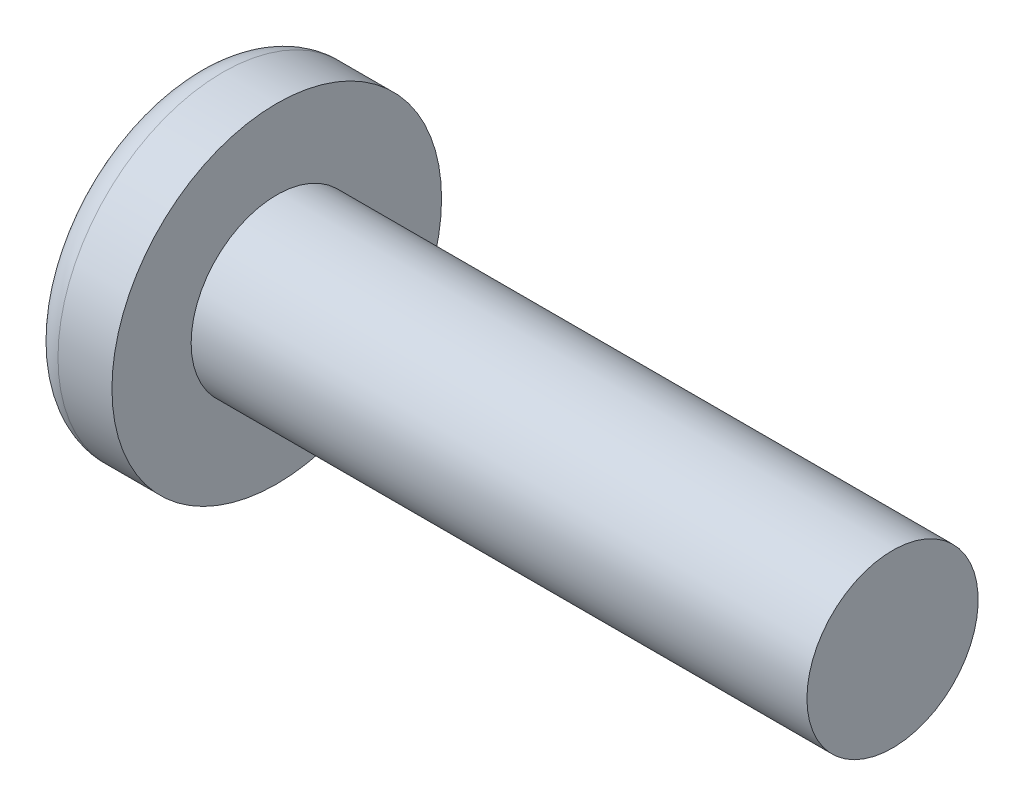
SolidWorks part; units mm, degrees
ref_plane "Plane1" through (0, 0, 0) normal (0, 0, 1) x (1, 0, 0)
ref_plane "Plane2" through (0, 0, 0) normal (0, 1, 0) x (1, 0, 0)
ref_plane "Plane3" through (0, 0, 0) normal (1, 0, 0) x (0, 0, -1)
sketch "BodySke" plane through (0, 0, 0) normal (0, 0, 1) x (1, 0, 0)
  line L0 (1.35, 1.065) -> (1.35, 2.05)
  line L1 (1.85, 6.35) -> (1.85, -3.175) construction
  line L2 (-25.4, 0) -> (127, 0) construction
  line L3 (9.01, 0) -> (0, 0)
  line L4 (1.35, 1.065) -> (9.01, 1.065)
  line L5 (9.01, 1.065) -> (9.01, 0)
  line L6 (0.6787, 2.05) -> (1.35, 2.05)
  line L7 (1.35, -1.065) -> (9.01, -1.065) construction
  line L8 (1.35, 6.35) -> (1.35, -3.175) construction
  arc A0 (0.3434, 1.8211) -> (0, 0) centre (5, 0) ccw
  arc A2 (0.3434, 1.8211) -> (0.6787, 2.05) centre (0.6787, 1.69) cw
  dimension "Head_crown_rad" = 5
  dimension "Head_fillet_rad" = 0.36
  dimension "Diameter" = 2.13
  dimension "Length" = 7.66
  dimension "Head_ht" = 1.35
  dimension "Head_dia" = 4.1
  dimension "Advance" = 0.5
  dimension "Thread_nom" = 7.66
revolve "Base-Revolve" add sketch "BodySke" angle 360 about L2
cosmetic thread "ThreadCosmetic" [suppressed] parameters "Thread_length"=7.16, "Thread_minor"=2.439
sketch "Sketch3" plane through (0, 0, 0) normal (1, 0, 0) x (0, 0, -1)
  line L0 (0.37, -1.45) -> (-0.37, -1.45)
  line L1 (0.37, -1.45) -> (0.37, 1.45)
  line L2 (-0.37, 1.45) -> (0.37, 1.45)
  line L3 (-0.37, 1.45) -> (-0.37, -1.45)
  dimension "Cross_dia" = 2.9
  dimension "D1" = 1.45
  dimension "Cross_width" = 0.74
  dimension "D2" = 0.37
ref_plane "Plane4" through (1.76, 0, 0) normal (1, 0, 0) x (0, 0, -1)
sketch "Sketch4" plane through (1.76, 0, 0) normal (1, 0, 0) x (0, 0, -1)
  line L0 (0.185, -0.185) -> (-0.185, -0.185)
  line L1 (0.185, -0.185) -> (0.185, 0.185)
  line L2 (-0.185, 0.185) -> (0.185, 0.185)
  line L3 (-0.185, 0.185) -> (-0.185, -0.185)
  dimension "D2" = 0.37
  dimension "D1" = 0.37
  dimension "D3" = 0.185
  dimension "D4" = 0.185
loft "Cut-Loft1" cut profiles "Sketch3", "Sketch4"
pattern_circular "CirPattern1" count 2 every 90 about axis through (0, 0, 0) along (1, 0, 0) of "Cut-Loft1"
sketch "ThdSchSke" plane through (0, 0, 0) normal (0, 0, 1) x (1, 0, 0)
  line L0 (1.85, -1.2195) -> (1.9582, -1.065)
  line L1 (1.85, -1.2195) -> (1.7418, -1.065)
  line L2 (1.7418, -1.065) -> (1.7418, -1.3312)
  line L3 (-3.175, 0) -> (5.1513, 0) construction
  line L5 (1.7418, -1.3312) -> (1.9582, -1.3312)
  line L6 (1.9582, -1.3312) -> (1.9582, -1.065)
  dimension "Diameter" = 2.13
  dimension "SideAngle" = 55
  dimension "VeeAngle" = 70
  dimension "Thread_minor" = 2.439
  dimension "Overcut" = 2.6625
  dimension "Start" = 1.85
revolve "ThreadSchematic" [suppressed] cut sketch "ThdSchSke" angle 360 about L3
pattern_linear "ThdSchPat" [suppressed]
equation "\"D1@Sketch3\" = \"Cross_dia@Sketch3\" / 2"
equation "\"D2@Sketch3\" = \"Cross_width@Sketch3\" / 2"
equation "\"D1@Sketch4\" = \"Cross_width@Sketch3\" *.5"
equation "\"D2@Sketch4\" = \"D1@Sketch4\""
equation "\"D3@Sketch4\" = \"D1@Sketch4\" / 2"
equation "\"D4@Sketch4\" = \"D2@Sketch4\" / 2"
equation "\"Thread_length@ThreadCosmetic\" = ((sgn( (\"Length@BodySke\" - \"Advance@BodySke\" ) - \"Thread_nom@BodySke\" )-1)*( (\"Length@BodySke\" - \"Advance@BodySke\" ) - \"Thread_nom@BodySke\" ))/-2+ \"Thread_nom@BodySke\""
equation "\"Thread_minor@ThdSchSke\" = \"Thread_minor@ThreadCosmetic\""
equation "\"Diameter@ThdSchSke\" = \"Diameter@BodySke\""
equation "\"Overcut@ThdSchSke\" = \"Diameter@BodySke\" * 1.25"
equation "\"Start@ThdSchSke\" = \"Head_ht@BodySke\" + \"Length@BodySke\" - \"Thread_length@ThreadCosmetic\"  '---Non-countersunk---"
equation "\"Num_threads@ThdSchPat\" = int( \"Thread_length@ThreadCosmetic\" / \"Advance@BodySke\" + 0.999 )  + 1"
equation "\"Advance@ThdSchPat\" = \"Thread_length@ThreadCosmetic\" /  (\"Num_threads@ThdSchPat\" - 1) 'relax it"
